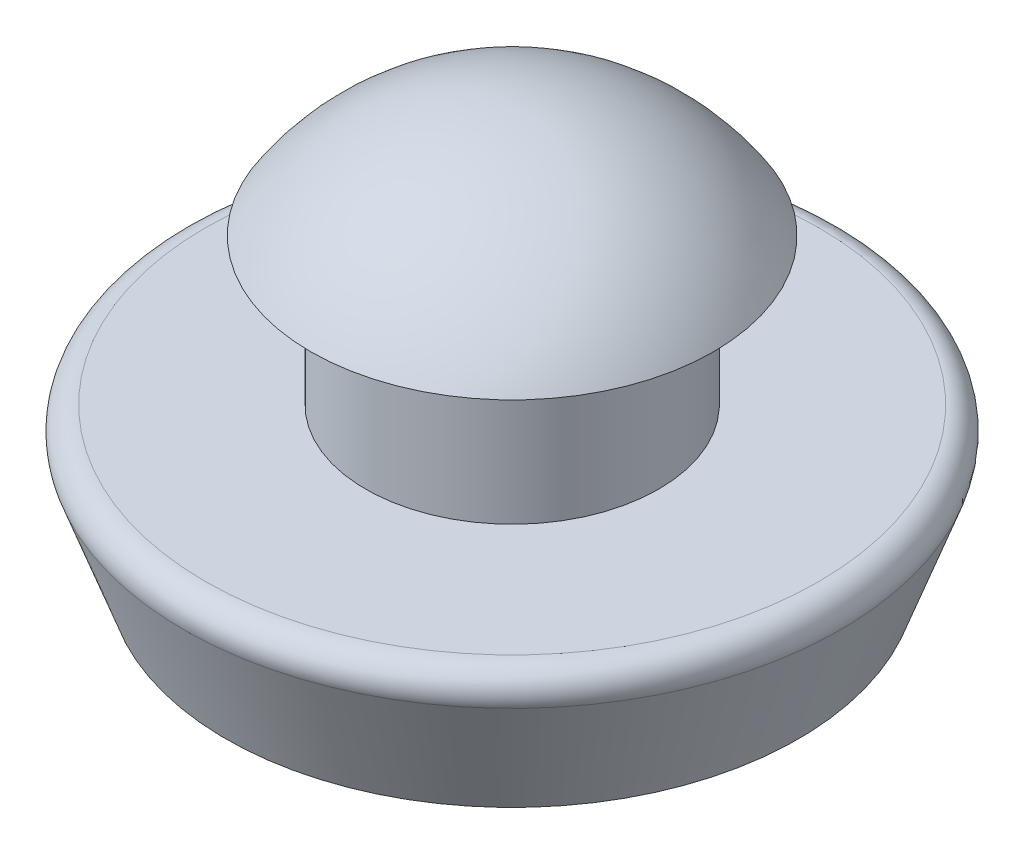
SolidWorks part; units mm, degrees
ref_plane "Front Plane" through (0, 0, 0) normal (0, 0, 1) x (1, 0, 0)
ref_plane "Top Plane" through (0, 0, 0) normal (0, 1, 0) x (1, 0, 0)
ref_plane "Right Plane" through (0, 0, 0) normal (1, 0, 0) x (0, 0, -1)
sketch "Sketch1" plane through (0, 0, 0) normal (0, 0, 1) x (1, 0, 0)
  line L0 (0, 5.5562) -> (0, -3.175)
  line L1 (0, -3.175) -> (-6.2022, -3.175)
  line L2 (-6.2022, -3.175) -> (-7.1136, -0.671)
  line L3 (-6.6438, 0) -> (-3.175, 0)
  line L4 (-3.175, 0) -> (-3.175, 3.175)
  line L5 (-3.175, 3.175) -> (-4.3656, 3.175)
  line L6 (-4.3656, 3.175) -> (4.3656, 3.175) construction
  line L7 (-7.1438, 0) -> (-7.1437, -3.175) construction
  line L8 (-7.1437, -3.175) -> (7.1438, -3.175) construction
  line L9 (7.1438, -3.175) -> (7.1438, 0) construction
  line L10 (7.1438, 0) -> (-7.1438, 0) construction
  line L11 (3.175, 3.175) -> (3.175, 0) construction
  arc A0 (-4.3656, 3.175) -> (0, 5.5562) centre (0, 0.3638) cw
  arc A1 (-6.6438, 0) -> (-7.1136, -0.671) centre (-6.6438, -0.5) ccw
  dimension "D4" = 0.5
  dimension "D1" = 14.2875
  dimension "D2" = 3.175
  dimension "D3" = 8.7312
  dimension "D5" = 20
  dimension "D6" = 6.35
  dimension "D7" = 3.175
  dimension "D8" = 2.3813
revolve "Revolve1" add sketch "Sketch1" angle 360 about L0
sketch "Sketch2" plane through (0, 0, 0) normal (0, 1, 0) x (1, 0, 0)
  circle A0 centre (0, 0) radius 3.175
  circle A1 centre (0, 0) radius 7.5 construction
  circle A2 centre (0, 0) radius 4.5 construction
  dimension "D1" = 6.35
  dimension "D2" = 15
  dimension "D3" = 9
  dimension "D4" = 3
